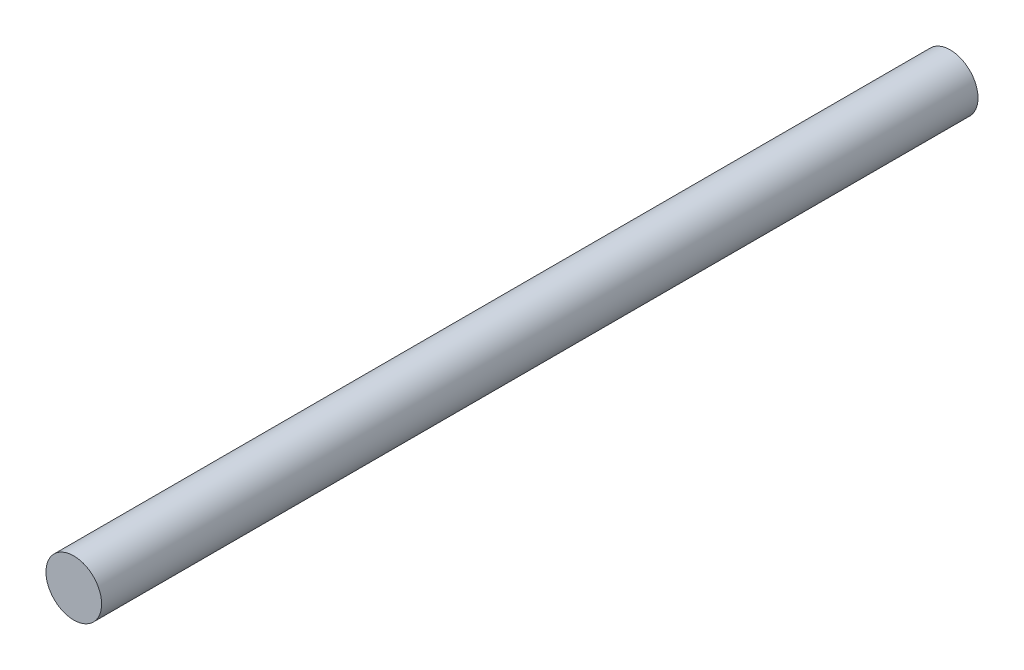
SolidWorks part; units mm, degrees
ref_plane "Front Plane" through (0, 0, 0) normal (0, 0, 1) x (1, 0, 0)
ref_plane "Top Plane" through (0, 0, 0) normal (0, 1, 0) x (1, 0, 0)
ref_plane "Right Plane" through (0, 0, 0) normal (1, 0, 0) x (0, 0, -1)
sketch "Sketch1" plane through (0, 0, 0) normal (0, 0, 1) x (1, 0, 0)
  circle A0 centre (0, 0) radius 3.175
  dimension "D1" = 6.35
extrude "Boss-Extrude1" add sketch "Sketch1" along normal blind 100
